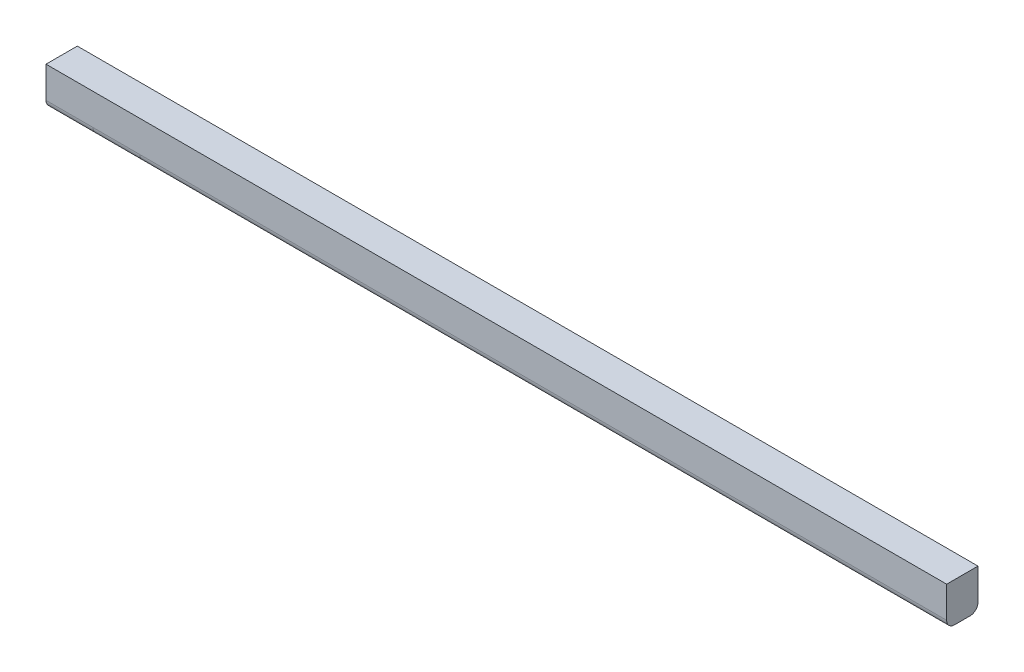
SolidWorks part; units mm, degrees
ref_plane "Ebene vorne" through (0, 0, 0) normal (0, 0, 1) x (1, 0, 0)
ref_plane "Ebene oben" through (0, 0, 0) normal (0, 1, 0) x (1, 0, 0)
ref_plane "Ebene rechts" through (0, 0, 0) normal (1, 0, 0) x (0, 0, -1)
sketch "Skizze1" plane through (0, 0, 0) normal (1, 0, 0) x (0, 0, -1)
  line L1 (-3, 0) -> (1, 0)
  line L2 (-3, 0) -> (-3, -5)
  line L3 (-3, -5) -> (1, -5)
  line L4 (1, 0) -> (1, -5)
  dimension "D1" = 4
  dimension "D2" = 3
  dimension "D3" = 5
  dimension "D4" = 5
extrude "Aufsatz-Linear austragen1" add sketch "Skizze1" along normal blind 115
sketch "Skizze2" plane through (0, 0, 0) normal (0, 1, 0) x (1, 0, 0)
  line L0 (115, -3) -> (0, -3) construction
  line L1 (0, 1) -> (0, -3) construction
  circle A0 centre (3, -1) radius 1.5
  dimension "D1" = 3
  dimension "D2" = 3
  dimension "D3" = 2
fillet "Verrundung1" radius 1 2 edges at (57.5, -5, -1) (57.5, -5, 3)
sketch "Skizze3" plane through (0, -5, 0) normal (0, -1, 0) x (1, 0, 0)
  line L0 (115, 2) -> (0, 2) construction
  line L1 (6, 3) -> (12, 3)
  line L2 (6, 3) -> (6, -1)
  line L3 (6, -1) -> (12, -1)
  line L4 (12, 3) -> (12, -1)
  line L5 (0, 0) -> (115, 0) construction
  line L6 (0, 2) -> (0, 0) construction
  line L7 (115, 2) -> (115, 0) construction
  line L8 (102, 2) -> (106, 2)
  line L9 (102, 2) -> (102, 0)
  line L10 (102, 0) -> (106, 0)
  line L11 (106, 2) -> (106, 0)
  line L12 (115, -1) -> (0, -1) construction
  line L13 (0, 3) -> (115, 3) construction
  dimension "D1" = 6
  dimension "D2" = 6
  dimension "D3" = 4
  dimension "D4" = 9
  dimension "D5" = 0
  dimension "D6" = 0
split line "Trennlinie1"
sketch3d "3D-Skizze1"
  line L4 (106, -5, 2) -> (102, -5, 2)
  line L5 (106, -5, 0) -> (106, -5, 2)
  line L6 (102, -5, 0) -> (106, -5, 0)
  line L7 (102, -5, 2) -> (102, -5, 0)
  line L8 (106, -5, 2) -> (102, -5, 2)
  line L9 (106, -5, 0) -> (106, -5, 2)
  line L10 (102, -5, 0) -> (106, -5, 0)
  line L11 (102, -5, 2) -> (102, -5, 0)
  line L12 (12, -5, 3) -> (6, -5, 3)
  line L13 (12, -5, -1) -> (12, -5, 3)
  line L14 (6, -5, -1) -> (12, -5, -1)
  line L15 (6, -5, 3) -> (6, -5, -1)
  line L16 (12, -5, 3) -> (6, -5, 3)
  line L17 (12, -5, -1) -> (12, -5, 3)
  line L18 (6, -5, -1) -> (12, -5, -1)
  line L19 (6, -5, 3) -> (6, -5, -1)
  dimension "D1" = 0
  dimension "D2" = 0
ref_plane "Ebene1" through (6, 0, 0) normal (-1, 0, 0) x (0, 0, 1)
ref_plane "Ebene2" through (12, 0, 0) normal (-1, 0, 0) x (0, 0, 1)
sketch "Skizze4" plane through (6, 0, 0) normal (-1, 0, 0) x (0, 0, 1)
  line L0 (0, -5) -> (2, -5)
  arc A0 (0, -5) -> (-1, -4) centre (0, -4) cw
  arc A1 (2, -5) -> (3, -4) centre (2, -4) ccw
  arc A2 (2, -5) -> (3, -4) centre (2, -4) ccw construction
sketch "Skizze5" plane through (12, 0, 0) normal (-1, 0, 0) x (0, 0, 1)
  line L0 (0, -5) -> (2, -5)
  arc A0 (0, -5) -> (-1, -4) centre (0, -4) cw
  arc A1 (2, -5) -> (3, -4) centre (2, -4) ccw
split line "Trennlinie7"
